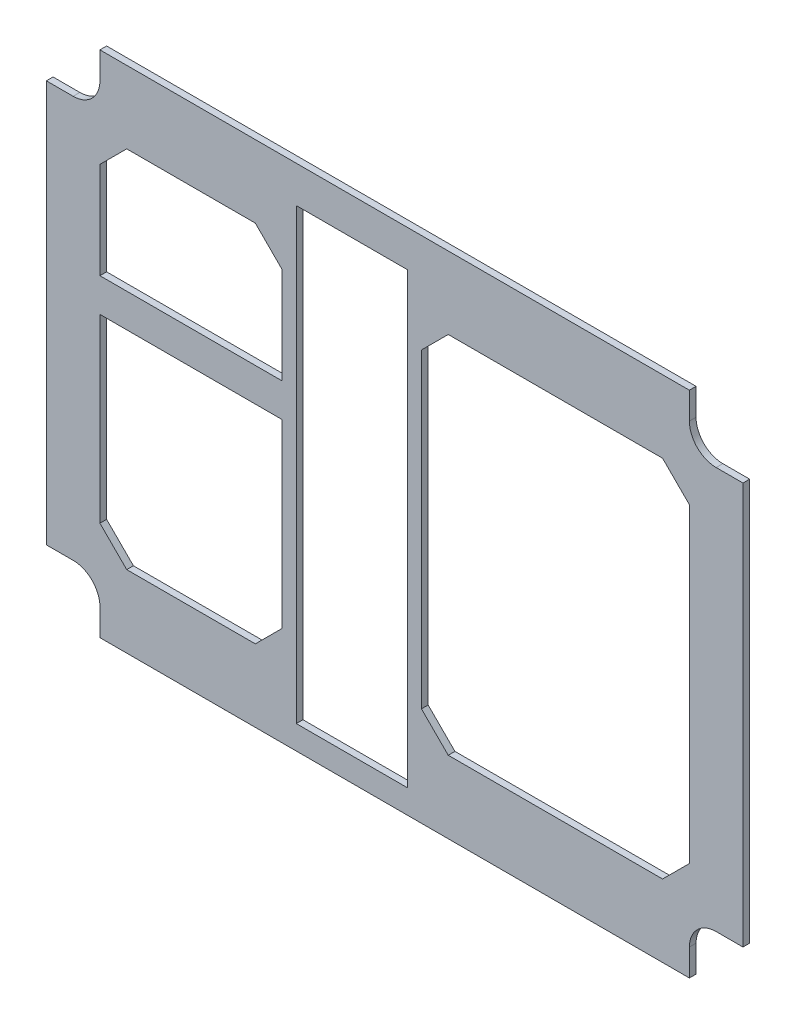
SolidWorks part; units mm, degrees
ref_plane "Front Plane" through (0, 0, 0) normal (0, 0, 1) x (1, 0, 0)
ref_plane "Top Plane" through (0, 0, 0) normal (0, 1, 0) x (1, 0, 0)
ref_plane "Right Plane" through (0, 0, 0) normal (1, 0, 0) x (0, 0, -1)
sketch "Sketch1" plane through (0, 0, 0) normal (0, 0, 1) x (1, 0, 0)
  line L0 (0, -12.7) -> (-6.35, -12.7) construction
  line L1 (-12.7, -6.35) -> (-12.7, 0) construction
  line L2 (-12.7, 0) -> (-152.4, 0) construction
  line L3 (-152.4, 0) -> (-152.4, -6.35) construction
  line L4 (-158.75, -12.7) -> (-165.1, -12.7) construction
  line L5 (-165.1, -12.7) -> (-165.1, -107.95) construction
  line L6 (-165.1, -107.95) -> (-158.75, -107.95) construction
  line L7 (-152.4, -114.3) -> (-152.4, -120.65) construction
  line L8 (-152.4, -120.65) -> (-12.7, -120.65) construction
  line L9 (-12.7, -120.65) -> (-12.7, -114.3) construction
  line L10 (-6.35, -107.95) -> (0, -107.95) construction
  line L11 (0, -107.95) -> (0, -12.7) construction
  line L12 (-102.87, -112.014) -> (-82.55, -112.014) construction
  line L13 (-82.55, -112.014) -> (-82.55, -11.684) construction
  line L14 (-82.55, -11.684) -> (-102.87, -11.684) construction
  line L15 (-102.87, -11.684) -> (-102.87, -112.014) construction
  line L16 (-19.05, -17.145) -> (-69.85, -17.145) construction
  line L17 (-69.85, -17.145) -> (-76.2, -23.495) construction
  line L18 (-76.2, -23.495) -> (-76.2, -97.155) construction
  line L19 (-76.2, -97.155) -> (-69.85, -103.505) construction
  line L20 (-69.85, -103.505) -> (-19.05, -103.505) construction
  line L21 (-19.05, -103.505) -> (-12.7, -97.155) construction
  line L22 (-12.7, -97.155) -> (-12.7, -23.495) construction
  line L23 (-12.7, -23.495) -> (-19.05, -17.145) construction
  line L24 (-152.4, -23.495) -> (-152.4, -46.355) construction
  line L25 (-152.4, -46.355) -> (-109.22, -46.355) construction
  line L26 (-109.22, -46.355) -> (-109.22, -23.495) construction
  line L27 (-109.22, -23.495) -> (-115.57, -17.145) construction
  line L28 (-115.57, -17.145) -> (-146.05, -17.145) construction
  line L29 (-146.05, -17.145) -> (-152.4, -23.495) construction
  line L30 (-109.22, -97.155) -> (-109.22, -54.2925) construction
  line L31 (-109.22, -54.2925) -> (-152.4, -54.2925) construction
  line L32 (-152.4, -54.2925) -> (-152.4, -97.155) construction
  line L33 (-152.4, -97.155) -> (-146.05, -103.505) construction
  line L34 (-146.05, -103.505) -> (-115.57, -103.505) construction
  line L35 (-115.57, -103.505) -> (-109.22, -97.155) construction
  line L36 (0, -12.7) -> (-6.35, -12.7)
  line L37 (-12.7, -6.35) -> (-12.7, 0)
  line L38 (-12.7, 0) -> (-152.4, 0)
  line L39 (-152.4, 0) -> (-152.4, -6.35)
  line L40 (-158.75, -12.7) -> (-165.1, -12.7)
  line L41 (-165.1, -12.7) -> (-165.1, -107.95)
  line L42 (-165.1, -107.95) -> (-158.75, -107.95)
  line L43 (-152.4, -114.3) -> (-152.4, -120.65)
  line L44 (-152.4, -120.65) -> (-12.7, -120.65)
  line L45 (-12.7, -120.65) -> (-12.7, -114.3)
  line L46 (-6.35, -107.95) -> (0, -107.95)
  line L47 (0, -107.95) -> (0, -12.7)
  line L48 (-102.87, -112.014) -> (-82.55, -112.014)
  line L49 (-82.55, -112.014) -> (-82.55, -11.684)
  line L50 (-82.55, -11.684) -> (-102.87, -11.684)
  line L51 (-102.87, -11.684) -> (-102.87, -112.014)
  line L52 (-19.05, -17.145) -> (-69.85, -17.145)
  line L53 (-69.85, -17.145) -> (-76.2, -23.495)
  line L54 (-76.2, -23.495) -> (-76.2, -97.155)
  line L55 (-76.2, -97.155) -> (-69.85, -103.505)
  line L56 (-69.85, -103.505) -> (-19.05, -103.505)
  line L57 (-19.05, -103.505) -> (-12.7, -97.155)
  line L58 (-12.7, -97.155) -> (-12.7, -23.495)
  line L59 (-12.7, -23.495) -> (-19.05, -17.145)
  line L60 (-152.4, -23.495) -> (-152.4, -46.355)
  line L61 (-152.4, -46.355) -> (-109.22, -46.355)
  line L62 (-109.22, -46.355) -> (-109.22, -23.495)
  line L63 (-109.22, -23.495) -> (-115.57, -17.145)
  line L64 (-115.57, -17.145) -> (-146.05, -17.145)
  line L65 (-146.05, -17.145) -> (-152.4, -23.495)
  line L66 (-109.22, -97.155) -> (-109.22, -54.2925)
  line L67 (-109.22, -54.2925) -> (-152.4, -54.2925)
  line L68 (-152.4, -54.2925) -> (-152.4, -97.155)
  line L69 (-152.4, -97.155) -> (-146.05, -103.505)
  line L70 (-146.05, -103.505) -> (-115.57, -103.505)
  line L71 (-115.57, -103.505) -> (-109.22, -97.155)
  arc A0 (-12.7, -6.35) -> (-6.35, -12.7) centre (-6.35, -6.35) ccw construction
  arc A1 (-158.75, -12.7) -> (-152.4, -6.35) centre (-158.75, -6.35) ccw construction
  arc A2 (-152.4, -114.3) -> (-158.75, -107.95) centre (-158.75, -114.3) ccw construction
  arc A3 (-6.35, -107.95) -> (-12.7, -114.3) centre (-6.35, -114.3) ccw construction
  arc A4 (-12.7, -6.35) -> (-6.35, -12.7) centre (-6.35, -6.35) ccw
  arc A5 (-158.75, -12.7) -> (-152.4, -6.35) centre (-158.75, -6.35) ccw
  arc A6 (-152.4, -114.3) -> (-158.75, -107.95) centre (-158.75, -114.3) ccw
  arc A7 (-6.35, -107.95) -> (-12.7, -114.3) centre (-6.35, -114.3) ccw
extrude "Boss-Extrude1" add sketch "Sketch1" along normal blind 1.5875
sketch "Sketch2" plane through (0, 0, 0) normal (0, 0, -1) x (-1, 0, 0)
  line L9 (105.87, -115.014) -> (105.87, -8.684)
  line L10 (79.55, -115.014) -> (105.87, -115.014)
  line L11 (79.55, -8.684) -> (79.55, -115.014)
  line L12 (105.87, -8.684) -> (79.55, -8.684)
  line L13 (105.87, -115.014) -> (105.87, -8.684)
  line L14 (79.55, -115.014) -> (105.87, -115.014)
  line L15 (79.55, -8.684) -> (79.55, -115.014)
  line L16 (105.87, -8.684) -> (79.55, -8.684)
  dimension "D1" = 3
extrude "Cut-Extrude1" cut sketch "Sketch2" against normal through all
